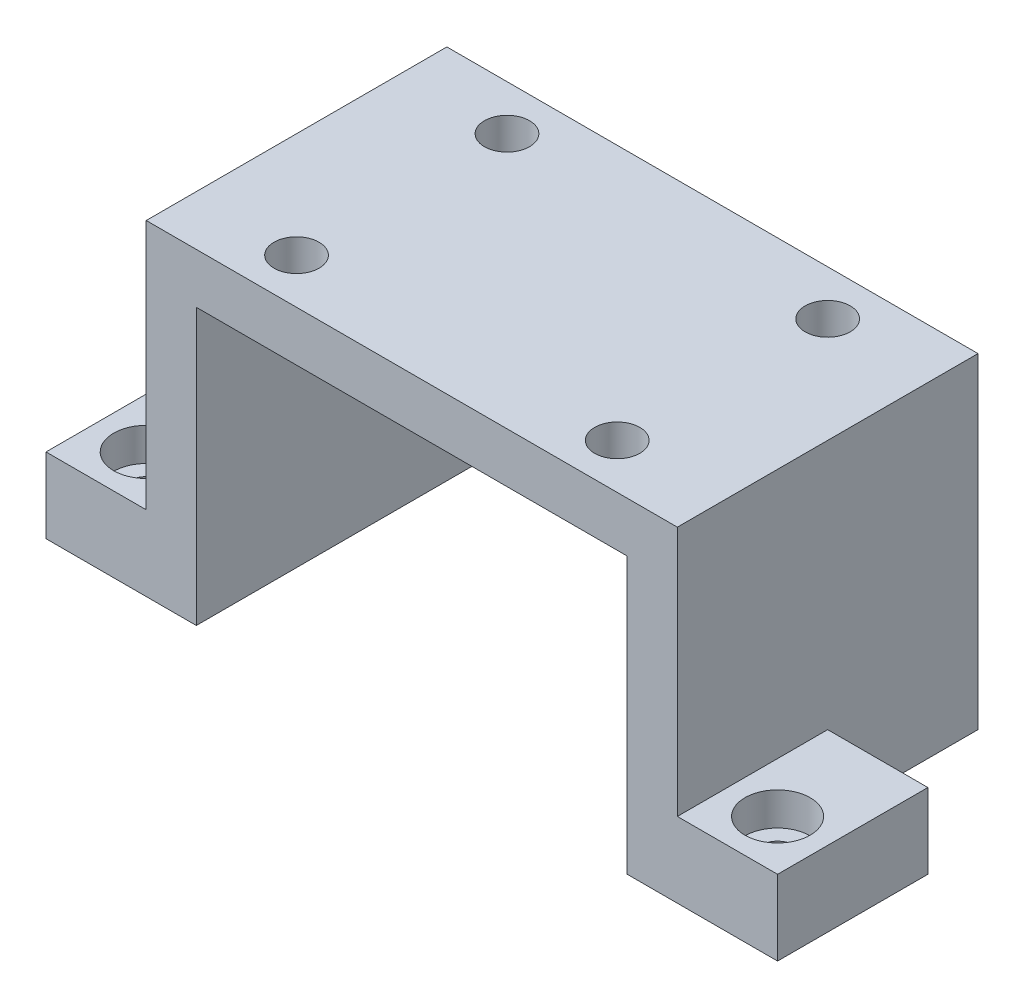
SolidWorks part; units mm, degrees
material "1.0045 (S355JR)"
ref_plane "Front Plane" through (0, 0, 0) normal (0, 0, 1) x (1, 0, 0)
ref_plane "Top Plane" through (0, 0, 0) normal (0, 1, 0) x (1, 0, 0)
ref_plane "Right Plane" through (0, 0, 0) normal (1, 0, 0) x (0, 0, -1)
sketch "Sketch1" plane through (0, 0, 0) normal (0, 1, 0) x (1, 0, 0)
  line L1 (-53, -30) -> (53, -30)
  line L2 (-53, -30) -> (-53, 30)
  line L3 (-53, 30) -> (53, 30)
  line L4 (53, -30) -> (53, 30)
  line L5 (-53, -30) -> (53, 30) construction
  line L6 (-53, 30) -> (53, -30) construction
  point P0 (0, 0)
  dimension "D1" = 60
  dimension "D2" = 106
extrude "Boss-Extrude1" add sketch "Sketch1" along normal blind 10
sketch "Sketch2" plane through (0, 0, 0) normal (0, -1, 0) x (1, 0, 0)
  line L0 (53, -30) -> (-53, -30) construction
  line L1 (-53, 30) -> (-43, 30)
  line L2 (-53, 30) -> (-53, -30)
  line L3 (-53, -30) -> (-43, -30)
  line L4 (-43, 30) -> (-43, -30)
  line L6 (53, 30) -> (43, 30)
  line L7 (53, 30) -> (53, -30)
  line L8 (53, -30) -> (43, -30)
  line L9 (43, 30) -> (43, -30)
  dimension "D1" = 10
  dimension "D2" = 10
extrude "Boss-Extrude2" add sketch "Sketch2" along normal blind 55
sketch "Sketch3" plane through (53, 0, 0) normal (1, 0, 0) x (0, 0, -1)
  line L1 (-30, -55) -> (0, -55)
  line L2 (-30, -55) -> (-30, -40)
  line L3 (-30, -40) -> (0, -40)
  line L5 (0, -40) -> (0, -55)
  dimension "D1" = 15
  dimension "D2" = 30
extrude "Boss-Extrude3" add sketch "Sketch3" along normal blind 20
sketch "Sketch4" plane through (-53, 0, 0) normal (-1, 0, 0) x (0, 0, 1)
  line L0 (30, 10) -> (30, -55) construction
  line L1 (-30, -55) -> (30, -55)
  line L2 (-30, -55) -> (-30, -40)
  line L3 (-30, -40) -> (30, -40)
  line L4 (30, -55) -> (30, -40)
  dimension "D1" = 15
extrude "Boss-Extrude4" add sketch "Sketch4" along normal blind 20
sketch "Sketch5" plane through (0, 10, 0) normal (0, 1, 0) x (1, 0, 0)
  line L0 (0, 0) -> (0, 30) construction
  line L1 (53, 30) -> (-53, 30) construction
  line L2 (0, 0) -> (18.8591, 0) construction
  circle A0 centre (-32, 21) radius 4.5
  circle A1 centre (32, 21) radius 4.5
  circle A2 centre (32, -21) radius 4.5
  circle A3 centre (-32, -21) radius 4.5
  dimension "D3" = 9
  dimension "D1" = 32
  dimension "D2" = 21
extrude "Cut-Extrude1" cut sketch "Sketch5" against normal through all
sketch "Sketch6" plane through (0, -40, 0) normal (0, 1, 0) x (1, 0, 0)
  line L1 (73, 0) -> (73, -30) construction
  line L2 (73, -30) -> (53, -30) construction
  line L3 (-73, -30) -> (-73, 30) construction
  line L4 (-73, 30) -> (-53, 30) construction
  line L5 (-73, -30) -> (-53, -30) construction
  circle A1 centre (63, -20) radius 6.5
  circle A2 centre (-63, 20) radius 6.5
  circle A3 centre (-63, -20) radius 6.5
  dimension "D9" = 13
  dimension "D10" = 13
  dimension "D12" = 13
  dimension "D3" = 10
  dimension "D4" = 10
  dimension "D5" = 10
  dimension "D6" = 10
  dimension "D7" = 10
  dimension "D8" = 10
extrude "Cut-Extrude2" cut sketch "Sketch6" against normal blind 6.6
sketch "Sketch7" plane through (0, -46.6, 0) normal (0, 1, 0) x (1, 0, 0)
  circle A0 centre (-63, 20) radius 3.3
  circle A1 centre (-63, -20) radius 3.3
  circle A2 centre (63, -20) radius 3.3
  dimension "D1" = 6.6
  dimension "D2" = 6.6
  dimension "D4" = 6.6
extrude "Cut-Extrude3" cut sketch "Sketch7" against normal through all
